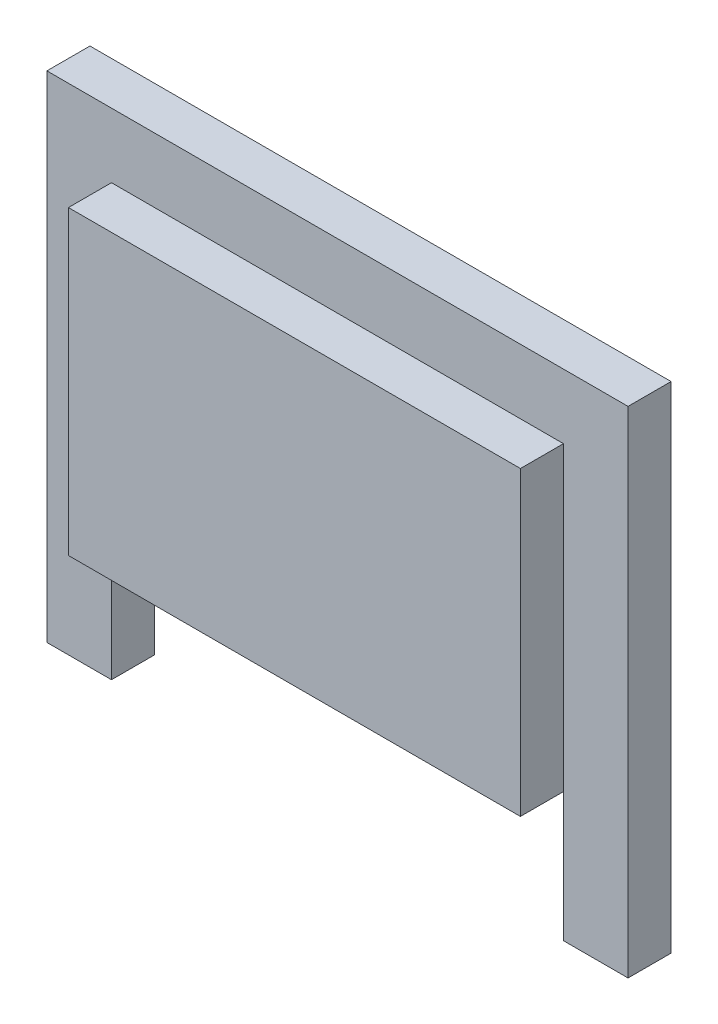
SolidWorks part; units mm, degrees
ref_plane "Front Plane" through (0, 0, 0) normal (0, 0, 1) x (1, 0, 0)
ref_plane "Top Plane" through (0, 0, 0) normal (0, 1, 0) x (1, 0, 0)
ref_plane "Right Plane" through (0, 0, 0) normal (1, 0, 0) x (0, 0, -1)
sketch "Sketch1" plane through (0, 0, 0) normal (0, 0, 1) x (1, 0, 0)
  line L1 (-13.5, -11.5) -> (13.5, -11.5)
  line L2 (-13.5, -11.5) -> (-13.5, 11.5)
  line L3 (-13.5, 11.5) -> (13.5, 11.5)
  line L4 (13.5, -11.5) -> (13.5, 11.5)
  line L5 (-13.5, -11.5) -> (13.5, 11.5) construction
  line L6 (-13.5, 11.5) -> (13.5, -11.5) construction
  point P0 (0, 0)
  dimension "D1" = 27
  dimension "D2" = 23
extrude "Boss-Extrude1" add sketch "Sketch1" along normal blind 2
sketch "Sketch2" plane through (0, 0, 2) normal (0, 0, 1) x (1, 0, 0)
  line L0 (13.5, 11.5) -> (-13.5, 11.5) construction
  line L1 (-10.5, 8.5) -> (10.5, 8.5)
  line L2 (-10.5, 8.5) -> (-10.5, -5.5)
  line L3 (-10.5, -5.5) -> (10.5, -5.5)
  line L4 (10.5, 8.5) -> (10.5, -5.5)
  line L5 (13.5, -11.5) -> (13.5, 11.5) construction
  line L6 (-13.5, 11.5) -> (-13.5, -11.5) construction
  dimension "D1" = 3
  dimension "D2" = 3
  dimension "D3" = 3
  dimension "D4" = 14
extrude "Boss-Extrude2" add sketch "Sketch2" along normal blind 2
sketch "Sketch3" plane through (0, 0, 2) normal (0, 0, 1) x (1, 0, 0)
  line L0 (-13.5, -11.5) -> (13.5, -11.5) construction
  line L1 (-10.5, -5.5) -> (10.5, -5.5)
  line L2 (-10.5, -5.5) -> (-10.5, -11.5)
  line L3 (-10.5, -11.5) -> (10.5, -11.5)
  line L4 (10.5, -5.5) -> (10.5, -11.5)
  line L5 (13.5, -11.5) -> (13.5, 11.5) construction
  dimension "D1" = 3
extrude "Cut-Extrude1" cut sketch "Sketch3" against normal blind 2
